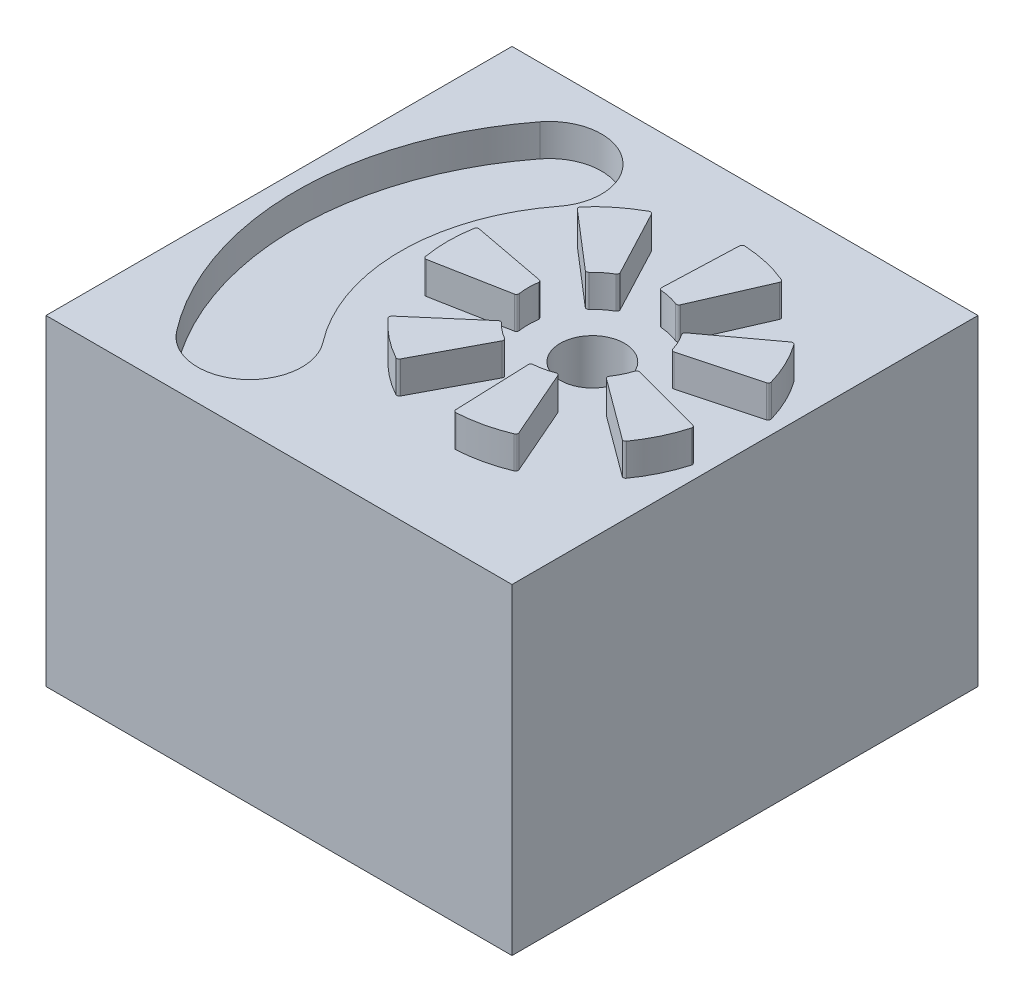
SolidWorks part; units mm, degrees
ref_plane "Front Plane" through (0, 0, 0) normal (0, 0, 1) x (1, 0, 0)
ref_plane "Top Plane" through (0, 0, 0) normal (0, 1, 0) x (1, 0, 0)
ref_plane "Right Plane" through (0, 0, 0) normal (1, 0, 0) x (0, 0, -1)
sketch "Sketch1" plane through (0, 0, 0) normal (0, 1, 0) x (1, 0, 0)
  line L1 (-46.0375, 46.0375) -> (46.0375, 46.0375)
  line L2 (-46.0375, 46.0375) -> (-46.0375, -46.0375)
  line L3 (-46.0375, -46.0375) -> (46.0375, -46.0375)
  line L4 (46.0375, 46.0375) -> (46.0375, -46.0375)
  dimension "D1" = 92.075
  dimension "D2" = 92.075
extrude "Boss-Extrude1" add sketch "Sketch1" against normal blind 63.5
sketch "Sketch3" plane through (0, 0, 0) normal (0, 1, 0) x (1, 0, 0)
  arc A0 (-14.0632, 23.2878) -> (-30.3868, 35.8942) centre (-22.225, 29.591) ccw
  arc A1 (-30.3868, -35.8942) -> (-14.0632, -23.2878) centre (-22.225, -29.591) ccw
  arc A3 (-30.3868, 35.8942) -> (-30.3868, -35.8942) centre (16.0912, 0) ccw
  arc A4 (-14.0632, 23.2878) -> (-14.0632, -23.2878) centre (16.0912, 0) ccw
extrude "Cut-Extrude1" cut sketch "Sketch3" against normal blind 6.35
sketch "Sketch4" plane through (0, 0, 0) normal (0, 1, 0) x (1, 0, 0)
  line L1 (42.9812, 7.2631) -> (28.6235, 3.416)
  line L2 (38.4535, 16.6646) -> (26.4941, 7.8376)
  line L3 (27.0969, 25.7209) -> (21.1529, 12.097)
  line L4 (16.9236, 28.0428) -> (16.3682, 13.189)
  line L5 (2.7623, 24.8104) -> (9.7079, 11.6688)
  line L6 (-5.396, 18.3042) -> (5.8709, 8.6088)
  line L7 (-11.6982, 5.2171) -> (2.9069, 2.4537)
  line L8 (-11.698, -5.2178) -> (2.9069, -2.454)
  line L9 (-5.3955, -18.3048) -> (5.8711, -8.609)
  line L10 (2.7629, -24.8107) -> (9.7082, -11.6689)
  line L11 (16.9243, -28.0428) -> (16.3685, -13.189)
  line L12 (27.0976, -25.7207) -> (21.1532, -12.0969)
  line L13 (38.4539, -16.664) -> (26.4943, -7.8374)
  line L14 (42.9814, -7.2624) -> (28.6236, -3.4156)
  arc A1 (28.0068, 3.7564) -> (26.3757, 7.1432) centre (15.875, 0) ccw
  arc A2 (20.5022, 11.8271) -> (16.8373, 12.6635) centre (15.875, 0) ccw
  arc A3 (43.3379, 7.8941) -> (39.1693, 16.5501) centre (15.875, 0) ccw
  arc A4 (26.826, 26.3933) -> (17.4594, 28.531) centre (15.875, 0) ccw
  arc A5 (26.3757, 7.1432) -> (26.4941, 7.8376) centre (26.7957, 7.4289) cw
  arc A6 (28.0068, 3.7564) -> (28.6235, 3.416) centre (28.492, 3.9066) ccw
  arc A7 (43.3379, 7.8941) -> (42.9812, 7.2631) centre (42.8497, 7.7538) cw
  arc A8 (38.4535, 16.6646) -> (39.1693, 16.5501) centre (38.7552, 16.2559) cw
  arc A9 (16.9236, 28.0428) -> (17.4594, 28.531) centre (17.4312, 28.0238) cw
  arc A10 (26.826, 26.3933) -> (27.0969, 25.7209) centre (26.6313, 25.9241) cw
  arc A11 (20.5022, 11.8271) -> (21.1529, 12.097) centre (20.6873, 12.3001) ccw
  arc A12 (16.8373, 12.6635) -> (16.3682, 13.189) centre (16.8758, 13.17) cw
  arc A13 (9.5132, 10.9917) -> (6.5743, 8.6479) centre (15.875, 0) ccw
  arc A14 (2.0677, 25.0178) -> (-5.4436, 19.0275) centre (15.875, 0) ccw
  arc A15 (-5.396, 18.3042) -> (-5.4436, 19.0275) centre (-5.0646, 18.6893) cw
  arc A16 (2.0677, 25.0178) -> (2.7623, 24.8104) centre (2.3132, 24.573) cw
  arc A17 (9.5132, 10.9917) -> (9.7079, 11.6688) centre (9.2588, 11.4314) ccw
  arc A18 (6.5743, 8.6479) -> (5.8709, 8.6088) centre (6.2023, 8.9938) cw
  arc A19 (3.3148, 1.8794) -> (3.3149, -1.8797) centre (15.875, 0) ccw
  arc A20 (-12.2934, 4.8034) -> (-12.2933, -4.8041) centre (15.875, 0) ccw
  arc A21 (-11.698, -5.2178) -> (-12.2933, -4.8041) centre (-11.7925, -4.7187) cw
  arc A22 (-12.2934, 4.8034) -> (-11.6982, 5.2171) centre (-11.7926, 4.718) cw
  arc A23 (3.3148, 1.8794) -> (2.9069, 2.4537) centre (2.8124, 1.9546) ccw
  arc A24 (3.3149, -1.8797) -> (2.9069, -2.454) centre (2.8125, -1.9549) cw
  arc A25 (6.5745, -8.6482) -> (9.5135, -10.9919) centre (15.875, 0) ccw
  arc A26 (-5.4431, -19.0281) -> (2.0684, -25.0181) centre (15.875, 0) ccw
  arc A27 (2.7629, -24.8107) -> (2.0684, -25.0181) centre (2.3138, -24.5734) cw
  arc A28 (-5.4431, -19.0281) -> (-5.3955, -18.3048) centre (-5.0641, -18.6898) cw
  arc A29 (6.5745, -8.6482) -> (5.8711, -8.609) centre (6.2025, -8.9941) ccw
  arc A30 (9.5135, -10.9919) -> (9.7082, -11.6689) centre (9.259, -11.4315) cw
  arc A31 (16.8376, -12.6635) -> (20.5025, -11.8269) centre (15.875, 0) ccw
  arc A32 (17.4601, -28.531) -> (26.8267, -26.393) centre (15.875, 0) ccw
  arc A33 (27.0976, -25.7207) -> (26.8267, -26.393) centre (26.632, -25.9238) cw
  arc A34 (17.4601, -28.531) -> (16.9243, -28.0428) centre (17.4319, -28.0238) cw
  arc A35 (16.8376, -12.6635) -> (16.3685, -13.189) centre (16.8761, -13.17) ccw
  arc A36 (20.5025, -11.8269) -> (21.1532, -12.0969) centre (20.6876, -12.3) cw
  arc A37 (26.3759, -7.1429) -> (28.0069, -3.7561) centre (15.875, 0) ccw
  arc A38 (39.1697, -16.5495) -> (43.3381, -7.8934) centre (15.875, 0) ccw
  arc A39 (42.9814, -7.2624) -> (43.3381, -7.8934) centre (42.8499, -7.7531) cw
  arc A40 (39.1697, -16.5495) -> (38.4539, -16.664) centre (38.7556, -16.2553) cw
  arc A41 (26.3759, -7.1429) -> (26.4943, -7.8374) centre (26.7959, -7.4286) ccw
  arc A42 (28.0069, -3.7561) -> (28.6236, -3.4156) centre (28.4921, -3.9063) cw
  point P92 (15.875, 0)
  dimension "D1" = 0.508
  dimension "D2" = 7
extrude "Boss-Extrude2" add sketch "Sketch4" along normal blind 6.35
sketch "Sketch5" plane through (0, 0, 0) normal (0, 1, 0) x (1, 0, 0)
  circle A0 centre (15.875, 0) radius 6.35
extrude "Cut-Extrude2" cut sketch "Sketch5" against normal blind 19.05
